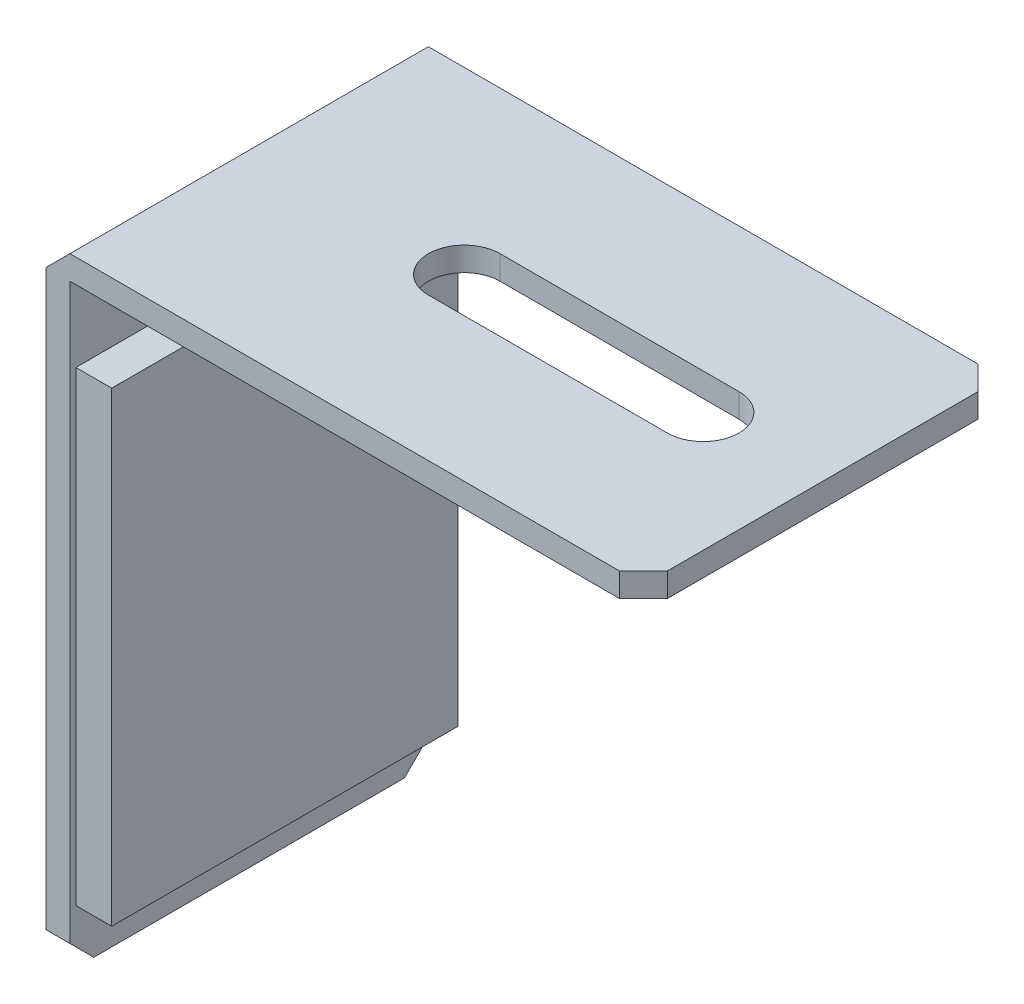
SolidWorks part; units mm, degrees
ref_plane "Plano frontal" through (0, 0, 0) normal (0, 0, 1) x (1, 0, 0)
ref_plane "Plano superior" through (0, 0, 0) normal (0, 1, 0) x (1, 0, 0)
ref_plane "Plano direito" through (0, 0, 0) normal (1, 0, 0) x (0, 0, -1)
sketch "Esboço1" plane through (0, 0, 0) normal (0, 0, 1) x (1, 0, 0)
  line L1 (0, 0) -> (2, 0)
  line L2 (0, 0) -> (0, 50)
  line L4 (2, 0) -> (2, 50)
  line L9 (0, 50) -> (50, 50)
  line L10 (0, 50) -> (0, 52)
  line L11 (0, 52) -> (50, 52)
  line L12 (50, 50) -> (50, 52)
extrude "Ressalto-extrusão1" add sketch "Esboço1" along normal blind 30 contours L9 L2 L1 L4 | L9 L12 L11 L10
chamfer "Chanfro1" distance 2 angle 45 5 edges at (1, 0, 0) (1, 0, 30) (50, 51, 0) (50, 51, 30) (0, 52, 15)
sketch "Esboço2" plane through (0, 52, 0) normal (0, 1, 0) x (1, 0, 0)
  line L1 (50, -15) -> (40, -15)
  line L2 (40, -15) -> (20, -15)
  line L3 (50, -28) -> (50, -2) construction
  line L4 (20, -12) -> (40, -12)
  line L5 (20, -12) -> (20, -18)
  line L6 (20, -18) -> (40, -18)
  line L7 (40, -12) -> (40, -18)
  circle A0 centre (40, -15) radius 3
  circle A1 centre (20, -15) radius 3
extrude "Corte-extrusão1" cut sketch "Esboço2" against normal blind 15
sketch "Esboço3" plane through (2, 0, 0) normal (1, 0, 0) x (0, 0, -1)
  line L0 (-15, 0) -> (-15, 4)
  line L1 (-28, 0) -> (-2, 0) construction
  line L2 (-30, 2) -> (-30, 50) construction
  line L3 (-30, 4) -> (0, 4)
  line L4 (-30, 4) -> (-30, 44)
  line L5 (-30, 44) -> (0, 44)
  line L6 (0, 4) -> (0, 44)
  line L7 (0, 2) -> (0, 50) construction
  line L8 (-29.5, 4.5) -> (-29.5, 43.5)
  line L9 (-29.5, 43.5) -> (-0.5, 43.5)
  line L10 (-0.5, 4.5) -> (-0.5, 43.5)
  line L11 (-29.5, 4.5) -> (-0.5, 4.5)
  dimension "D1" = 0.5
extrude "Ressalto-extrusão2" add sketch "Esboço3" along normal blind 3 contours L9 L10 L11 L8
